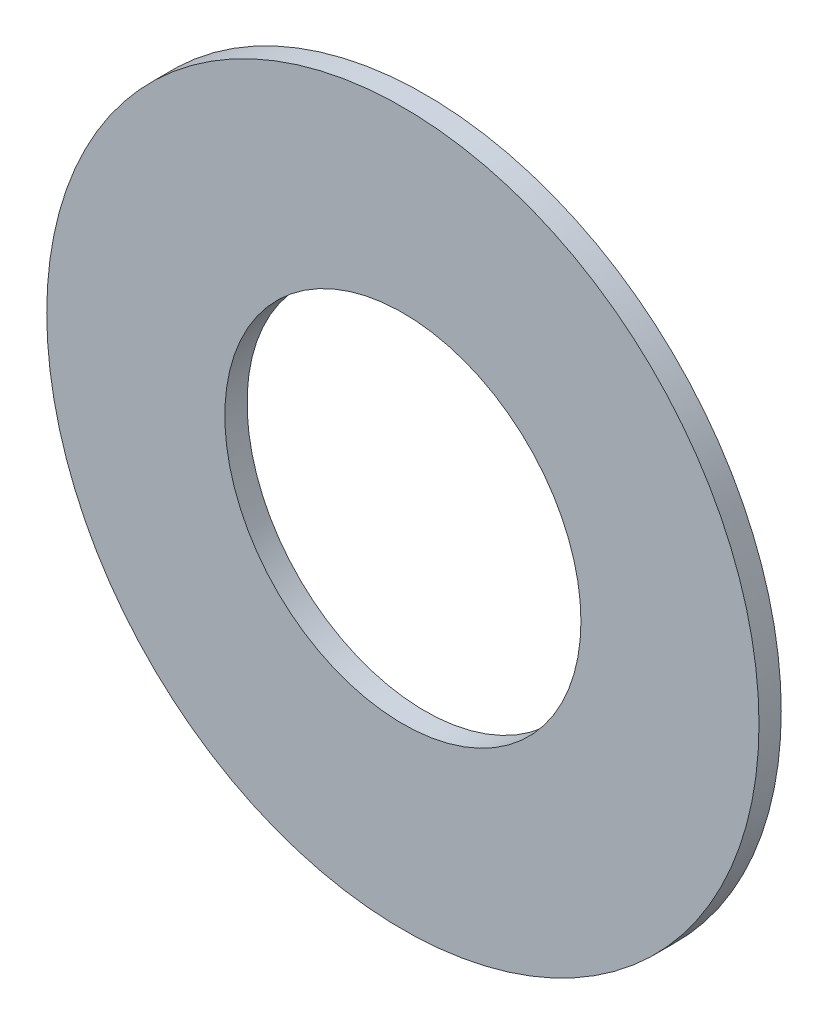
SolidWorks part; units mm, degrees
ref_plane "前视基准面" through (0, 0, 0) normal (0, 0, 1) x (1, 0, 0)
ref_plane "上视基准面" through (0, 0, 0) normal (0, 1, 0) x (1, 0, 0)
ref_plane "右视基准面" through (0, 0, 0) normal (1, 0, 0) x (0, 0, -1)
sketch "草图1" plane through (0, 0, 0) normal (0, 0, 1) x (1, 0, 0)
  circle A0 centre (0, 0) radius 4
  circle A1 centre (0, 0) radius 8
  dimension "D1" = 16
  dimension "D2" = 8
extrude "凸台-拉伸1" add sketch "草图1" along normal blind 0.5
